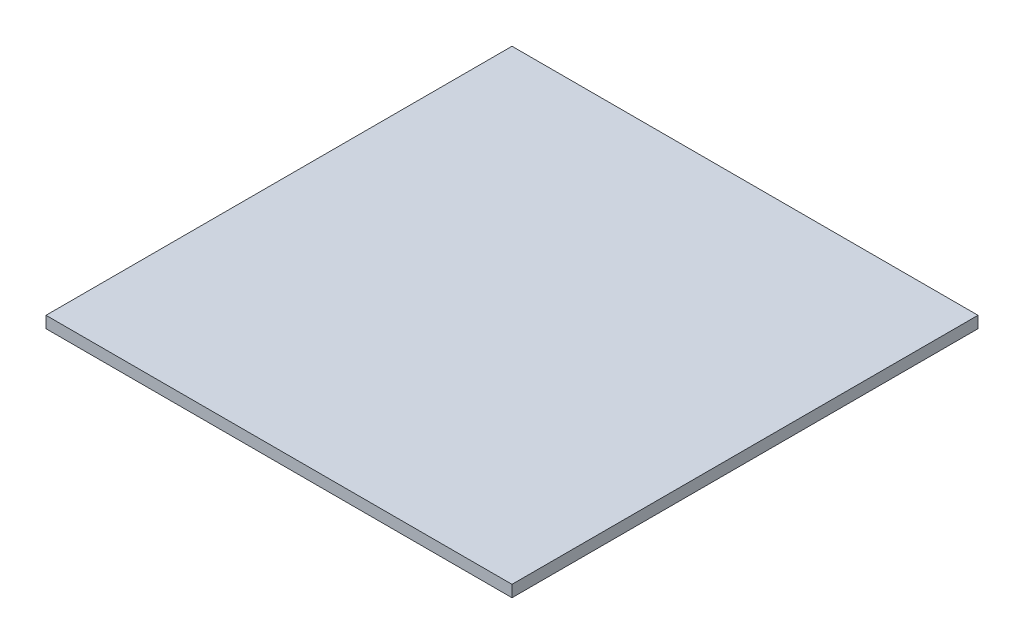
SolidWorks part; units mm, degrees
ref_plane "Front Plane" through (0, 0, 0) normal (0, 0, 1) x (1, 0, 0)
ref_plane "Top Plane" through (0, 0, 0) normal (0, 1, 0) x (1, 0, 0)
ref_plane "Right Plane" through (0, 0, 0) normal (1, 0, 0) x (0, 0, -1)
sketch "Sketch1" plane through (0, 0, 0) normal (0, 1, 0) x (1, 0, 0)
  line L0 (-200, 200) -> (200, -200) construction
  line L1 (-200, 200) -> (200, 200)
  line L2 (-200, 200) -> (-200, -200)
  line L3 (-200, -200) -> (200, -200)
  line L4 (200, 200) -> (200, -200)
  dimension "D1" = 400
  dimension "D2" = 400
extrude "Boss-Extrude1" add sketch "Sketch1" along normal blind 10
